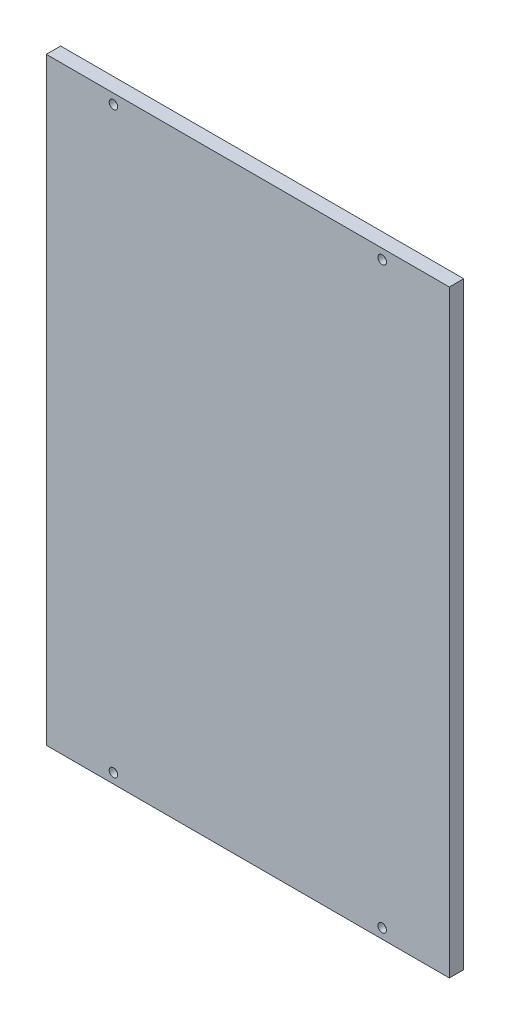
SolidWorks part; units mm, degrees
ref_plane "Plano frontal" through (0, 0, 0) normal (0, 0, 1) x (1, 0, 0)
ref_plane "Plano superior" through (0, 0, 0) normal (0, 1, 0) x (1, 0, 0)
ref_plane "Plano direito" through (0, 0, 0) normal (1, 0, 0) x (0, 0, -1)
sketch "Esboço1" plane through (0, 0, 0) normal (0, 0, 1) x (1, 0, 0)
  line L1 (150, -222.7) -> (-150, -222.7)
  line L2 (150, -222.7) -> (150, 222.7)
  line L3 (150, 222.7) -> (-150, 222.7)
  line L4 (-150, -222.7) -> (-150, 222.7)
  line L5 (150, -222.7) -> (-150, 222.7) construction
  line L6 (150, 222.7) -> (-150, -222.7) construction
  point P0 (0, 0)
  dimension "D1" = 445.4
  dimension "D2" = 300
extrude "Ressalto-extrusão1" add sketch "Esboço1" along normal blind 10.7
hole_wizard "Furo1" positions "Esboço2" profile "Esboço3" legacy end condition through all
sketch "Esboço2" plane through (0, 0, 0) normal (0, 0, -1) x (-1, 0, 0)
  line L0 (0, -143.2537) -> (0, 183.9483) construction
  line L2 (-106.5695, 0) -> (110.4436, 0) construction
  line L4 (-150, -222.7) -> (-150, 222.7) construction
  line L5 (-150, 222.7) -> (150, 222.7) construction
  point P0 (-100, 215.35)
  point P16 (-100, -215.35)
  point P18 (100, -215.35)
  point P19 (100, 215.35)
  dimension "D1" = 50
  dimension "D2" = 7.35
sketch "Esboço3" plane through (100, 215.35, 0) normal (1, 0, 0) x (0, 1, 0)
  line L0 (0, 0) -> (0, 10.7)
  line L1 (0, 10.7) -> (3.175, 10.7)
  line L2 (3.175, 10.7) -> (3.175, 6.35)
  line L3 (3.175, 6.35) -> (4.76, 6.35)
  line L4 (4.76, 6.35) -> (4.76, 0)
  line L5 (4.76, 0) -> (0, 0)
  line L6 (0, 110) -> (0, -10) construction
  dimension "Diameter" = 6.35
  dimension "Depth" = 10.7
  dimension "C-Bore Diameter" = 9.52
  dimension "C-Bore Depth" = 6.35
